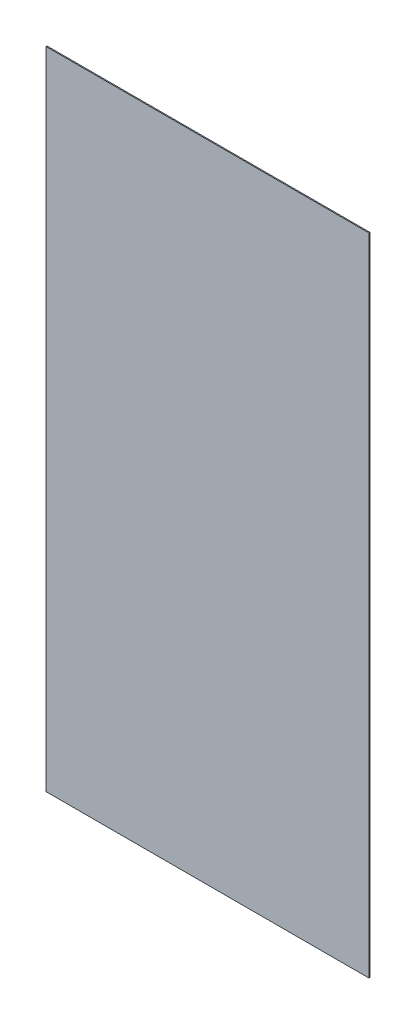
SolidWorks part; units mm, degrees
material "ABS"
ref_plane "Front" through (0, 0, 0) normal (0, 0, 1) x (1, 0, 0)
ref_plane "Top" through (0, 0, 0) normal (0, 1, 0) x (1, 0, 0)
ref_plane "Right" through (0, 0, 0) normal (1, 0, 0) x (0, 0, -1)
sketch "Sketch1" plane through (0, 0, 0) normal (0, 0, 1) x (1, 0, 0)
  line L1 (0, 0) -> (242.4, 0)
  line L2 (0, 0) -> (0, 484.8)
  line L3 (0, 484.8) -> (242.4, 484.8)
  line L4 (242.4, 0) -> (242.4, 484.8)
  dimension "D1" = 484.8
  dimension "D2" = 242.4
extrude "Boss-Extrude1" add sketch "Sketch1" along normal blind 0.75
